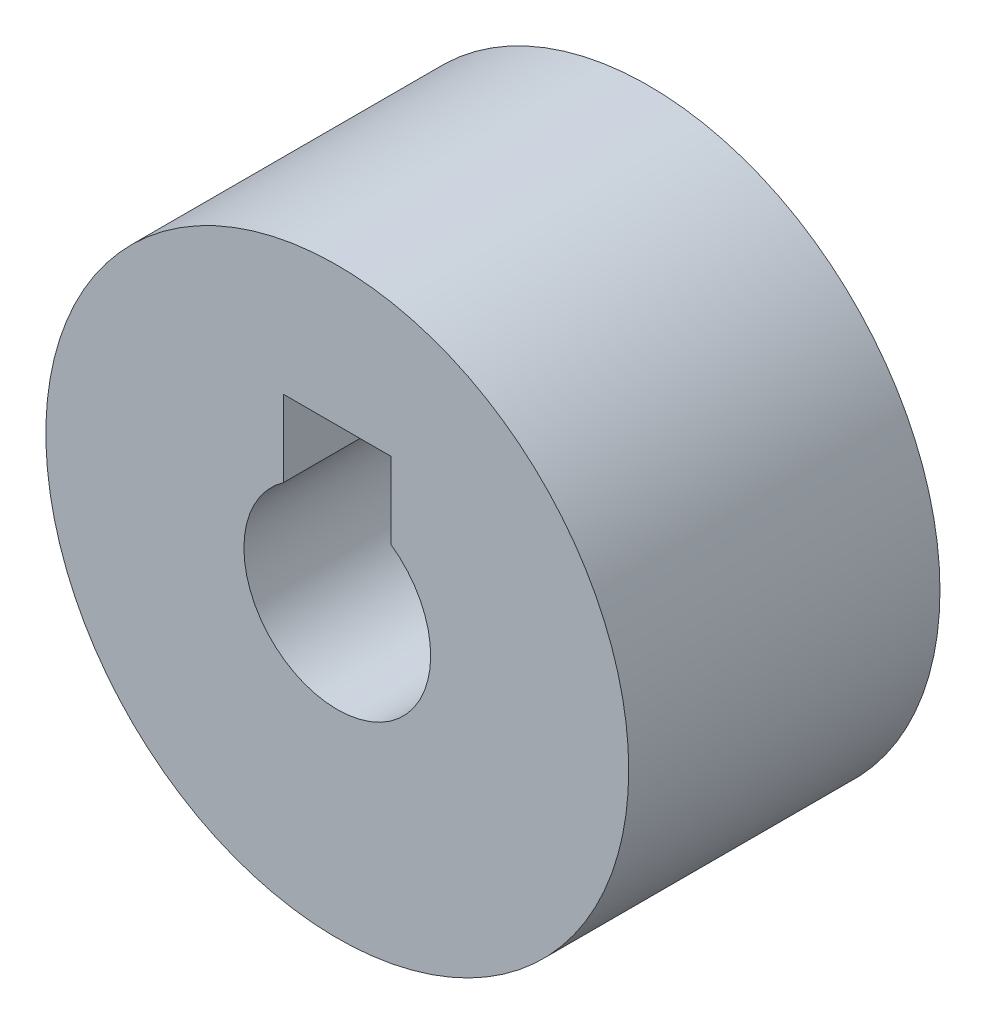
SolidWorks part; units mm, degrees
ref_plane "Front Plane" through (0, 0, 0) normal (0, 0, 1) x (1, 0, 0)
ref_plane "Top Plane" through (0, 0, 0) normal (0, 1, 0) x (1, 0, 0)
ref_plane "Right Plane" through (0, 0, 0) normal (1, 0, 0) x (0, 0, -1)
sketch "Sketch1" plane through (0, 0, 0) normal (0, 1, 0) x (1, 0, 0)
  line L0 (0, 0) -> (0, 2.7706) construction
  line L1 (5.15, 4.5699) -> (5.65, 4.5699)
  line L2 (1.65, 4.5699) -> (5.15, 4.5699)
  line L3 (1.65, 4.5699) -> (1.65, 1.5699)
  line L4 (1.65, 1.5699) -> (5.15, 1.5699)
  line L5 (5.15, 4.5699) -> (5.15, 1.5699)
  line L6 (5.65, 4.5699) -> (5.15, 3.0699)
  line L7 (5.15, 3.0699) -> (5.65, 1.5699)
  line L8 (5.65, 1.5699) -> (5.15, 1.5699)
  line L11 (1.65, 1.5699) -> (1.65, 1.8199)
  line L15 (1.65, 4.5699) -> (1.65, 5.3199)
  dimension "D1" = 1.65
  dimension "D2" = 3.5
  dimension "D3" = 0.5
  dimension "D4" = 0.5
  dimension "D7" = 3
revolve "Revolve1" add sketch "Sketch1" angle 360 about L0
sketch "Sketch2" plane through (0, 0, -1.5699) normal (0, 0, 1) x (1, 0, 0)
  circle A0 centre (0, 0) radius 3.2406
  circle A1 centre (0, 0) radius 4.5
  dimension "D1" = 9
sketch "Sketch3" plane through (0, 0, -4.5699) normal (0, 0, -1) x (-1, 0, 0)
  line L0 (2.5, 0) -> (-2.5, 0)
  line L1 (2.5, 4) -> (-2.5, 4)
  line L2 (2.5, 4) -> (2.5, -4)
  line L3 (2.5, -4) -> (-2.5, -4)
  line L4 (-2.5, 4) -> (-2.5, -4)
  line L5 (2.5, 4) -> (-2.5, -4) construction
  line L6 (2.5, -4) -> (-2.5, 4) construction
  circle A0 centre (0, 0) radius 1.65
  dimension "D1" = 8
  dimension "D2" = 5
extrude "Boss-Extrude1" [suppressed] add sketch "Sketch3" along normal blind 3
sketch "Sketch4" plane through (0, 0, -4.5699) normal (0, 0, -1) x (-1, 0, 0)
  line L0 (-1.9134, 4.6194) -> (1.9134, -4.6194)
  line L1 (-1.9134, -4.6194) -> (0, 0)
  line L2 (0, 0) -> (1.9134, 4.6194)
  line L5 (-4.6194, 1.9134) -> (4.6194, -1.9134)
  line L6 (-4.6194, -1.9134) -> (4.6194, 1.9134)
  circle A3 centre (0, 0) radius 5
  circle A5 centre (0, 0) radius 3.375
  dimension "D1" = 10
  dimension "D7" = 6.75
  dimension "D2" = 45
  dimension "D5" = 45
  dimension "D6" = 45
extrude "Cut-Extrude1" [suppressed] cut sketch "Sketch4" against normal blind 4
sketch "Sketch5" plane through (0, 0, -4.5699) normal (0, 0, -1) x (-1, 0, 0)
  line L0 (0.75, 0) -> (0.75, 1.4697)
  line L1 (-0.75, 0) -> (-0.75, 1.4697)
  circle A0 centre (0, 0) radius 0.75
  circle A1 centre (0, 0) radius 1.65 construction
  circle A2 centre (0, 0) radius 1.65
  dimension "D1" = 1.5
extrude "Boss-Extrude2" [suppressed] add sketch "Sketch5" against normal blind 3
sketch "Sketch6" plane through (0, 0, -1.5699) normal (0, 0, 1) x (1, 0, 0)
  line L1 (-0.95, 0) -> (0.95, 0)
  line L2 (-0.95, 0) -> (-0.95, 2.7)
  line L3 (-0.95, 2.7) -> (0.95, 2.7)
  line L4 (0.95, 0) -> (0.95, 2.7)
  circle A0 centre (0, 0) radius 0.95
  circle M10 centre (0, 0) radius 1.65
  dimension "D1" = 1.9
  dimension "D2" = 2.7
extrude "Cut-Extrude2" cut sketch "Sketch6" against normal blind 4 contours L4 L3 L2 M10
sketch "Sketch7" plane through (0, 0, -1.5699) normal (0, 0, 1) x (1, 0, 0)
  line L0 (0.95, 1.3491) -> (0.95, 2.7) construction
  line L1 (-0.95, 1.3491) -> (-0.95, 2.7) construction
  line L2 (-0.95, 2.7) -> (0.95, 2.7) construction
  line L3 (0.95, 1.3491) -> (0.95, 2.7)
  line L4 (-0.95, 1.3491) -> (-0.95, 2.7)
  line L5 (-0.95, 2.7) -> (0.95, 2.7)
  circle A0 centre (0, 0) radius 1.65
  circle A1 centre (0, 0) radius 5.15
  circle M1 centre (0, 0) radius 5.15
  arc M2 (0.95, 1.3491) -> (-0.95, 1.3491) centre (0, 0) cw
  line M3 (-0.95, 1.3491) -> (-0.95, 2.7)
  line M4 (-0.95, 2.7) -> (0.95, 2.7)
  line M5 (0.95, 2.7) -> (0.95, 1.3491)
extrude "Boss-Extrude3" add sketch "Sketch7" along normal blind 2.5 contours M1 M5 M2 M3 M4
